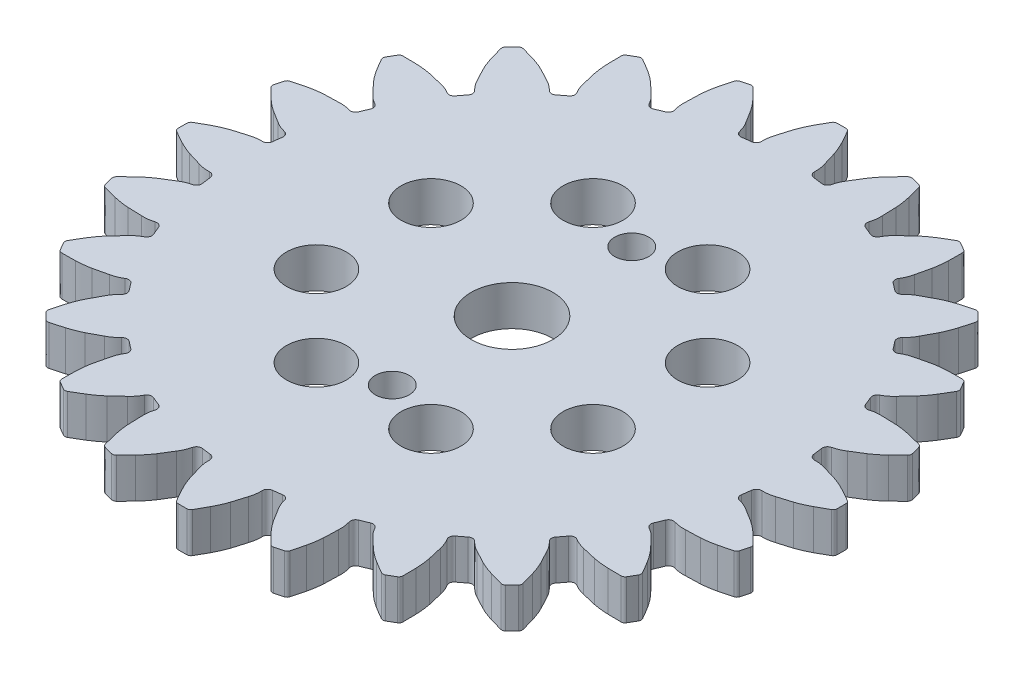
SolidWorks part; units mm, degrees
ref_plane "Front Plane" through (0, 0, 0) normal (0, 0, 1) x (1, 0, 0)
ref_plane "Top Plane" through (0, 0, 0) normal (0, 1, 0) x (1, 0, 0)
ref_plane "Right Plane" through (0, 0, 0) normal (1, 0, 0) x (0, 0, -1)
sketch "Sketch1" plane through (0, 0, 0) normal (0, 1, 0) x (1, 0, 0)
  line L0 (609.6, 337.82) -> (609.6, 271.78) construction
  line L1 (642.62, 304.8) -> (576.58, 304.8) construction
  arc A0 (636.7268, 307.9141) -> (636.6714, 308.364) centre (609.6, 304.8) ccw
  arc A1 (638.4674, 307.2733) -> (637.2762, 307.4442) centre (637.4121, 304.1554) ccw
  arc A2 (639.8524, 306.8554) -> (638.4674, 307.2733) centre (-758.3943, -4324.3767) ccw
  arc A3 (641.238, 306.2479) -> (639.8524, 306.8554) centre (637.042, 298.5613) ccw
  arc A4 (642.4176, 305.5857) -> (641.238, 306.2479) centre (614.8356, 257.8343) ccw
  arc A5 (642.62, 304.8) -> (642.617, 305.2456) centre (609.6, 304.8) ccw
  arc A6 (642.617, 305.2456) -> (642.4176, 305.5857) centre (642.218, 305.2402) ccw
  arc A7 (636.7268, 307.9141) -> (637.2762, 307.4442) centre (637.2542, 307.9746) ccw
  arc A8 (636.6714, 301.236) -> (636.7268, 301.6859) centre (609.6, 304.8) ccw
  arc A9 (637.2762, 302.1558) -> (638.4674, 302.3267) centre (637.4121, 305.4446) ccw
  arc A10 (638.4674, 302.3267) -> (639.8524, 302.7446) centre (-758.3943, 4933.9767) ccw
  arc A11 (639.8524, 302.7446) -> (641.238, 303.3521) centre (637.042, 311.0387) ccw
  arc A12 (641.238, 303.3521) -> (642.4176, 304.0143) centre (614.8356, 351.7657) ccw
  arc A13 (642.617, 304.3544) -> (642.62, 304.8) centre (609.6, 304.8) ccw
  arc A14 (642.4176, 304.0143) -> (642.617, 304.3544) centre (642.218, 304.3598) ccw
  arc A15 (637.2762, 302.1558) -> (636.7268, 301.6859) centre (637.2542, 301.6254) ccw
  arc A16 (636.6085, 300.787) -> (636.6714, 301.236) centre (609.6, 304.8) ccw
  arc A17 (638.1239, 299.7175) -> (637.0175, 300.191) centre (636.2976, 296.9791) ccw
  arc A18 (639.3535, 298.9554) -> (638.1239, 299.7175) centre (-1909.9001, -3812.5784) ccw
  arc A19 (640.5347, 298.01) -> (639.3535, 298.9554) centre (634.4923, 291.6714) ccw
  arc A20 (641.5027, 297.0651) -> (640.5347, 298.01) centre (602.5015, 258.0796) ccw
  arc A21 (641.4949, 296.2538) -> (641.6073, 296.6849) centre (609.6, 304.8) ccw
  arc A22 (641.6073, 296.6849) -> (641.5027, 297.0651) centre (641.2205, 296.783) ccw
  arc A23 (636.6085, 300.787) -> (637.0175, 300.191) centre (637.1336, 300.709) ccw
  arc A24 (634.8265, 294.3508) -> (634.9965, 294.7711) centre (609.6, 304.8) ccw
  arc A25 (635.6488, 295.0828) -> (636.8437, 294.9396) centre (636.6313, 298.2243) ccw
  arc A26 (636.8437, 294.9396) -> (638.2896, 294.9848) centre (486.3381, 5130.3043) ccw
  arc A27 (638.2896, 294.9848) -> (639.7852, 295.2129) centre (637.7216, 303.7236) ccw
  arc A28 (639.7852, 295.2129) -> (641.096, 295.5473) centre (626.8128, 348.8103) ccw
  arc A29 (641.3766, 295.8242) -> (641.4949, 296.2538) centre (609.6, 304.8) ccw
  arc A30 (641.096, 295.5473) -> (641.3766, 295.8242) centre (640.9927, 295.9327) ccw
  arc A31 (635.6488, 295.0828) -> (634.9965, 294.7711) centre (635.4903, 294.5761) ccw
  arc A32 (634.6496, 293.9334) -> (634.8265, 294.3508) centre (609.6, 304.8) ccw
  arc A33 (635.8366, 292.5082) -> (634.8904, 293.2519) centre (633.3637, 290.3357) ccw
  arc A34 (636.827, 291.4538) -> (635.8366, 292.5082) centre (-2889.7061, -3020.1875) ccw
  arc A35 (637.7232, 290.2349) -> (636.827, 291.4538) centre (630.2462, 285.6761) ccw
  arc A36 (638.4137, 289.0716) -> (637.7232, 290.2349) centre (590.6513, 261.5087) ccw
  arc A37 (638.1962, 288.29) -> (638.4163, 288.6774) centre (609.6, 304.8) ccw
  arc A38 (638.4163, 288.6774) -> (638.4137, 289.0716) centre (638.0681, 288.8722) ccw
  arc A39 (634.6496, 293.9334) -> (634.8904, 293.2519) centre (635.1366, 293.7222) ccw
  arc A40 (631.2625, 288.1778) -> (631.5355, 288.5397) centre (609.6, 304.8) ccw
  arc A41 (632.2462, 288.672) -> (633.3633, 288.2244) centre (634.0083, 291.4522) ccw
  arc A42 (633.3633, 288.2244) -> (634.7717, 287.8938) centre (1739.4706, 4997.7818) ccw
  arc A43 (634.7717, 287.8938) -> (636.2753, 287.7271) centre (636.4848, 296.4818) ccw
  arc A44 (636.2753, 287.7271) -> (637.6281, 287.7108) centre (637.617, 342.8557) ccw
  arc A45 (637.9708, 287.9056) -> (638.1962, 288.29) centre (609.6, 304.8) ccw
  arc A46 (637.6281, 287.7108) -> (637.9708, 287.9056) centre (637.628, 288.1098) ccw
  arc A47 (632.2462, 288.672) -> (631.5355, 288.5397) centre (631.962, 288.2236) ccw
  arc A48 (630.9836, 287.8204) -> (631.2625, 288.1778) centre (609.6, 304.8) ccw
  arc A49 (631.7612, 286.1365) -> (631.0397, 287.0997) centre (628.8104, 284.6781) ccw
  arc A50 (632.445, 284.8617) -> (631.7612, 286.1365) centre (-3631.0403, -2001.2042) ccw
  arc A51 (632.9952, 283.4524) -> (632.445, 284.8617) centre (624.593, 280.9842) ccw
  arc A52 (633.3611, 282.15) -> (632.9952, 283.4524) centre (580.0923, 267.8881) ccw
  arc A53 (632.9487, 281.4513) -> (633.2616, 281.7685) centre (609.6, 304.8) ccw
  arc A54 (633.2616, 281.7685) -> (633.3611, 282.15) centre (632.9757, 282.0468) ccw
  arc A55 (630.9836, 287.8204) -> (631.0397, 287.0997) centre (631.3993, 287.4903) ccw
  arc A56 (626.2222, 283.1375) -> (626.5796, 283.4164) centre (609.6, 304.8) ccw
  arc A57 (627.3003, 283.3603) -> (628.2635, 282.6388) centre (629.7219, 285.5896) ccw
  arc A58 (628.2635, 282.6388) -> (629.5383, 281.955) centre (2915.6042, 4545.4403) ccw
  arc A59 (629.5383, 281.955) -> (630.9476, 281.4048) centre (633.4158, 289.807) ccw
  arc A60 (630.9476, 281.4048) -> (632.25, 281.0389) centre (646.5119, 334.3077) ccw
  arc A61 (632.6315, 281.1384) -> (632.9487, 281.4513) centre (609.6, 304.8) ccw
  arc A62 (632.25, 281.0389) -> (632.6315, 281.1384) centre (632.3532, 281.4243) ccw
  arc A63 (627.3003, 283.3603) -> (626.5796, 283.4164) centre (626.9097, 283.0007) ccw
  arc A64 (625.8603, 282.8645) -> (626.2222, 283.1375) centre (609.6, 304.8) ccw
  arc A65 (626.1756, 281.0367) -> (625.728, 282.1538) centre (622.9478, 280.3917) ccw
  arc A66 (626.5062, 279.6283) -> (626.1756, 281.0367) centre (-4083.3818, -825.0706) ccw
  arc A67 (626.6729, 278.1247) -> (626.5062, 279.6283) centre (617.9182, 277.9152) ccw
  arc A68 (626.6892, 276.7719) -> (626.6729, 278.1247) centre (571.5443, 276.783) ccw
  arc A69 (626.11, 276.2038) -> (626.4944, 276.4292) centre (609.6, 304.8) ccw
  arc A70 (626.4944, 276.4292) -> (626.6892, 276.7719) centre (626.2902, 276.772) ccw
  arc A71 (625.8603, 282.8645) -> (625.728, 282.1538) centre (626.1764, 282.438) ccw
  arc A72 (620.0492, 279.5735) -> (620.4666, 279.7504) centre (609.6, 304.8) ccw
  arc A73 (621.1481, 279.5096) -> (621.8918, 278.5634) centre (624.0643, 281.0363) ccw
  arc A74 (621.8918, 278.5634) -> (622.9462, 277.573) centre (3934.5875, 3804.1061) ccw
  arc A75 (622.9462, 277.573) -> (624.1651, 276.6768) centre (628.7239, 284.1538) ccw
  arc A76 (624.1651, 276.6768) -> (625.3284, 275.9863) centre (652.8913, 323.7487) ccw
  arc A77 (625.7226, 275.9837) -> (626.11, 276.2038) centre (609.6, 304.8) ccw
  arc A78 (625.3284, 275.9863) -> (625.7226, 275.9837) centre (625.5278, 276.3319) ccw
  arc A79 (621.1481, 279.5096) -> (620.4666, 279.7504) centre (620.6778, 279.2634) ccw
  arc A80 (619.6289, 279.4035) -> (620.0492, 279.5735) centre (609.6, 304.8) ccw
  arc A81 (619.4604, 277.5563) -> (619.3172, 278.7512) centre (616.1757, 277.7687) ccw
  arc A82 (619.4152, 276.1104) -> (619.4604, 277.5563) centre (-4215.9043, 428.0619) ccw
  arc A83 (619.1871, 274.6148) -> (619.4152, 276.1104) centre (610.6764, 276.6784) ccw
  arc A84 (618.8527, 273.304) -> (619.1871, 274.6148) centre (565.5897, 287.5872) ccw
  arc A85 (618.1462, 272.9051) -> (618.5758, 273.0234) centre (609.6, 304.8) ccw
  arc A86 (618.5758, 273.0234) -> (618.8527, 273.304) centre (618.4673, 273.4073) ccw
  arc A87 (619.6289, 279.4035) -> (619.3172, 278.7512) centre (619.8239, 278.9097) ccw
  arc A88 (613.164, 277.7286) -> (613.613, 277.7915) centre (609.6, 304.8) ccw
  arc A89 (614.209, 277.3825) -> (614.6825, 276.2761) centre (617.4209, 278.1024) ccw
  arc A90 (614.6825, 276.2761) -> (615.4446, 275.0465) centre (4726.9784, 2824.3001) ccw
  arc A91 (615.4446, 275.0465) -> (616.39, 273.8653) centre (622.7286, 279.9077) ccw
  arc A92 (616.39, 273.8653) -> (617.3349, 272.8973) centre (656.3204, 311.8985) ccw
  arc A93 (617.7151, 272.7927) -> (618.1462, 272.9051) centre (609.6, 304.8) ccw
  arc A94 (617.3349, 272.8973) -> (617.7151, 272.7927) centre (617.617, 273.1795) ccw
  arc A95 (614.209, 277.3825) -> (613.613, 277.7915) centre (613.691, 277.2664) ccw
  arc A96 (612.7141, 277.6732) -> (613.164, 277.7286) centre (609.6, 304.8) ccw
  arc A97 (612.0733, 275.9326) -> (612.2442, 277.1238) centre (608.9554, 276.9879) ccw
  arc A98 (611.6554, 274.5476) -> (612.0733, 275.9326) centre (-4019.5767, 1672.7943) ccw
  arc A99 (611.0479, 273.162) -> (611.6554, 274.5476) centre (603.3613, 277.358) ccw
  arc A100 (610.3857, 271.9824) -> (611.0479, 273.162) centre (562.6343, 299.5644) ccw
  arc A101 (609.6, 271.78) -> (610.0456, 271.783) centre (609.6, 304.8) ccw
  arc A102 (610.0456, 271.783) -> (610.3857, 271.9824) centre (610.0402, 272.182) ccw
  arc A103 (612.7141, 277.6732) -> (612.2442, 277.1238) centre (612.7746, 277.1458) ccw
  arc A104 (606.036, 277.7286) -> (606.4859, 277.6732) centre (609.6, 304.8) ccw
  arc A105 (606.9558, 277.1238) -> (607.1267, 275.9326) centre (610.2446, 276.9879) ccw
  arc A106 (607.1267, 275.9326) -> (607.5446, 274.5476) centre (5238.7767, 1672.7943) ccw
  arc A107 (607.5446, 274.5476) -> (608.1521, 273.162) centre (615.8387, 277.358) ccw
  arc A108 (608.1521, 273.162) -> (608.8143, 271.9824) centre (656.5657, 299.5644) ccw
  arc A109 (609.1544, 271.783) -> (609.6, 271.78) centre (609.6, 304.8) ccw
  arc A110 (608.8143, 271.9824) -> (609.1544, 271.783) centre (609.1598, 272.182) ccw
  arc A111 (606.9558, 277.1238) -> (606.4859, 277.6732) centre (606.4254, 277.1458) ccw
  arc A112 (605.587, 277.7915) -> (606.036, 277.7286) centre (609.6, 304.8) ccw
  arc A113 (604.5175, 276.2761) -> (604.991, 277.3825) centre (601.7791, 278.1024) ccw
  arc A114 (603.7554, 275.0465) -> (604.5175, 276.2761) centre (-3507.7784, 2824.3001) ccw
  arc A115 (602.81, 273.8653) -> (603.7554, 275.0465) centre (596.4714, 279.9077) ccw
  arc A116 (601.8651, 272.8973) -> (602.81, 273.8653) centre (562.8796, 311.8985) ccw
  arc A117 (601.0538, 272.9051) -> (601.4849, 272.7927) centre (609.6, 304.8) ccw
  arc A118 (601.4849, 272.7927) -> (601.8651, 272.8973) centre (601.583, 273.1795) ccw
  arc A119 (605.587, 277.7915) -> (604.991, 277.3825) centre (605.509, 277.2664) ccw
  arc A120 (599.1508, 279.5735) -> (599.5711, 279.4035) centre (609.6, 304.8) ccw
  arc A121 (599.8828, 278.7512) -> (599.7396, 277.5563) centre (603.0243, 277.7687) ccw
  arc A122 (599.7396, 277.5563) -> (599.7848, 276.1104) centre (5435.1043, 428.0619) ccw
  arc A123 (599.7848, 276.1104) -> (600.0129, 274.6148) centre (608.5236, 276.6784) ccw
  arc A124 (600.0129, 274.6148) -> (600.3473, 273.304) centre (653.6103, 287.5872) ccw
  arc A125 (600.6242, 273.0234) -> (601.0538, 272.9051) centre (609.6, 304.8) ccw
  arc A126 (600.3473, 273.304) -> (600.6242, 273.0234) centre (600.7327, 273.4073) ccw
  arc A127 (599.8828, 278.7512) -> (599.5711, 279.4035) centre (599.3761, 278.9097) ccw
  arc A128 (598.7334, 279.7504) -> (599.1508, 279.5735) centre (609.6, 304.8) ccw
  arc A129 (597.3082, 278.5634) -> (598.0519, 279.5096) centre (595.1357, 281.0363) ccw
  arc A130 (596.2538, 277.573) -> (597.3082, 278.5634) centre (-2715.3875, 3804.1061) ccw
  arc A131 (595.0349, 276.6768) -> (596.2538, 277.573) centre (590.4761, 284.1538) ccw
  arc A132 (593.8716, 275.9863) -> (595.0349, 276.6768) centre (566.3087, 323.7487) ccw
  arc A133 (593.09, 276.2038) -> (593.4774, 275.9837) centre (609.6, 304.8) ccw
  arc A134 (593.4774, 275.9837) -> (593.8716, 275.9863) centre (593.6722, 276.3319) ccw
  arc A135 (598.7334, 279.7504) -> (598.0519, 279.5096) centre (598.5222, 279.2634) ccw
  arc A136 (592.9778, 283.1375) -> (593.3397, 282.8645) centre (609.6, 304.8) ccw
  arc A137 (593.472, 282.1538) -> (593.0244, 281.0367) centre (596.2522, 280.3917) ccw
  arc A138 (593.0244, 281.0367) -> (592.6938, 279.6283) centre (5302.5818, -825.0706) ccw
  arc A139 (592.6938, 279.6283) -> (592.5271, 278.1247) centre (601.2818, 277.9152) ccw
  arc A140 (592.5271, 278.1247) -> (592.5108, 276.7719) centre (647.6557, 276.783) ccw
  arc A141 (592.7056, 276.4292) -> (593.09, 276.2038) centre (609.6, 304.8) ccw
  arc A142 (592.5108, 276.7719) -> (592.7056, 276.4292) centre (592.9098, 276.772) ccw
  arc A143 (593.472, 282.1538) -> (593.3397, 282.8645) centre (593.0236, 282.438) ccw
  arc A144 (592.6204, 283.4164) -> (592.9778, 283.1375) centre (609.6, 304.8) ccw
  arc A145 (590.9365, 282.6388) -> (591.8997, 283.3603) centre (589.4781, 285.5896) ccw
  arc A146 (589.6617, 281.955) -> (590.9365, 282.6388) centre (-1696.4042, 4545.4403) ccw
  arc A147 (588.2524, 281.4048) -> (589.6617, 281.955) centre (585.7842, 289.807) ccw
  arc A148 (586.95, 281.0389) -> (588.2524, 281.4048) centre (572.6881, 334.3077) ccw
  arc A149 (586.2513, 281.4513) -> (586.5685, 281.1384) centre (609.6, 304.8) ccw
  arc A150 (586.5685, 281.1384) -> (586.95, 281.0389) centre (586.8468, 281.4243) ccw
  arc A151 (592.6204, 283.4164) -> (591.8997, 283.3603) centre (592.2903, 283.0007) ccw
  arc A152 (587.9375, 288.1778) -> (588.2164, 287.8204) centre (609.6, 304.8) ccw
  arc A153 (588.1603, 287.0997) -> (587.4388, 286.1365) centre (590.3896, 284.6781) ccw
  arc A154 (587.4388, 286.1365) -> (586.755, 284.8617) centre (4850.2403, -2001.2042) ccw
  arc A155 (586.755, 284.8617) -> (586.2048, 283.4524) centre (594.607, 280.9842) ccw
  arc A156 (586.2048, 283.4524) -> (585.8389, 282.15) centre (639.1077, 267.8881) ccw
  arc A157 (585.9384, 281.7685) -> (586.2513, 281.4513) centre (609.6, 304.8) ccw
  arc A158 (585.8389, 282.15) -> (585.9384, 281.7685) centre (586.2243, 282.0468) ccw
  arc A159 (588.1603, 287.0997) -> (588.2164, 287.8204) centre (587.8007, 287.4903) ccw
  arc A160 (587.6645, 288.5397) -> (587.9375, 288.1778) centre (609.6, 304.8) ccw
  arc A161 (585.8367, 288.2244) -> (586.9538, 288.672) centre (585.1917, 291.4522) ccw
  arc A162 (584.4283, 287.8938) -> (585.8367, 288.2244) centre (-520.2706, 4997.7818) ccw
  arc A163 (582.9247, 287.7271) -> (584.4283, 287.8938) centre (582.7152, 296.4818) ccw
  arc A164 (581.5719, 287.7108) -> (582.9247, 287.7271) centre (581.583, 342.8557) ccw
  arc A165 (581.0038, 288.29) -> (581.2292, 287.9056) centre (609.6, 304.8) ccw
  arc A166 (581.2292, 287.9056) -> (581.5719, 287.7108) centre (581.572, 288.1098) ccw
  arc A167 (587.6645, 288.5397) -> (586.9538, 288.672) centre (587.238, 288.2236) ccw
  arc A168 (584.3735, 294.3508) -> (584.5504, 293.9334) centre (609.6, 304.8) ccw
  arc A169 (584.3096, 293.2519) -> (583.3634, 292.5082) centre (585.8363, 290.3357) ccw
  arc A170 (583.3634, 292.5082) -> (582.373, 291.4538) centre (4108.9061, -3020.1875) ccw
  arc A171 (582.373, 291.4538) -> (581.4768, 290.2349) centre (588.9538, 285.6761) ccw
  arc A172 (581.4768, 290.2349) -> (580.7863, 289.0716) centre (628.5487, 261.5087) ccw
  arc A173 (580.7837, 288.6774) -> (581.0038, 288.29) centre (609.6, 304.8) ccw
  arc A174 (580.7863, 289.0716) -> (580.7837, 288.6774) centre (581.1319, 288.8722) ccw
  arc A175 (584.3096, 293.2519) -> (584.5504, 293.9334) centre (584.0634, 293.7222) ccw
  arc A176 (584.2035, 294.7711) -> (584.3735, 294.3508) centre (609.6, 304.8) ccw
  arc A177 (582.3563, 294.9396) -> (583.5512, 295.0828) centre (582.5687, 298.2243) ccw
  arc A178 (580.9104, 294.9848) -> (582.3563, 294.9396) centre (732.8619, 5130.3043) ccw
  arc A179 (579.4148, 295.2129) -> (580.9104, 294.9848) centre (581.4784, 303.7236) ccw
  arc A180 (578.104, 295.5473) -> (579.4148, 295.2129) centre (592.3872, 348.8103) ccw
  arc A181 (577.7051, 296.2538) -> (577.8234, 295.8242) centre (609.6, 304.8) ccw
  arc A182 (577.8234, 295.8242) -> (578.104, 295.5473) centre (578.2073, 295.9327) ccw
  arc A183 (584.2035, 294.7711) -> (583.5512, 295.0828) centre (583.7097, 294.5761) ccw
  arc A184 (582.5286, 301.236) -> (582.5915, 300.787) centre (609.6, 304.8) ccw
  arc A185 (582.1825, 300.191) -> (581.0761, 299.7175) centre (582.9024, 296.9791) ccw
  arc A186 (581.0761, 299.7175) -> (579.8465, 298.9554) centre (3129.1001, -3812.5784) ccw
  arc A187 (579.8465, 298.9554) -> (578.6653, 298.01) centre (584.7077, 291.6714) ccw
  arc A188 (578.6653, 298.01) -> (577.6973, 297.0651) centre (616.6985, 258.0796) ccw
  arc A189 (577.5927, 296.6849) -> (577.7051, 296.2538) centre (609.6, 304.8) ccw
  arc A190 (577.6973, 297.0651) -> (577.5927, 296.6849) centre (577.9795, 296.783) ccw
  arc A191 (582.1825, 300.191) -> (582.5915, 300.787) centre (582.0664, 300.709) ccw
  arc A192 (582.4732, 301.6859) -> (582.5286, 301.236) centre (609.6, 304.8) ccw
  arc A193 (580.7326, 302.3267) -> (581.9238, 302.1558) centre (581.7879, 305.4446) ccw
  arc A194 (579.3476, 302.7446) -> (580.7326, 302.3267) centre (1977.5943, 4933.9767) ccw
  arc A195 (577.962, 303.3521) -> (579.3476, 302.7446) centre (582.158, 311.0387) ccw
  arc A196 (576.7824, 304.0143) -> (577.962, 303.3521) centre (604.3644, 351.7657) ccw
  arc A197 (576.58, 304.8) -> (576.583, 304.3544) centre (609.6, 304.8) ccw
  arc A198 (576.583, 304.3544) -> (576.7824, 304.0143) centre (576.982, 304.3598) ccw
  arc A199 (582.4732, 301.6859) -> (581.9238, 302.1558) centre (581.9458, 301.6254) ccw
  arc A200 (582.5286, 308.364) -> (582.4732, 307.9141) centre (609.6, 304.8) ccw
  arc A201 (581.9238, 307.4442) -> (580.7326, 307.2733) centre (581.7879, 304.1554) ccw
  arc A202 (580.7326, 307.2733) -> (579.3476, 306.8554) centre (1977.5943, -4324.3767) ccw
  arc A203 (579.3476, 306.8554) -> (577.962, 306.2479) centre (582.158, 298.5613) ccw
  arc A204 (577.962, 306.2479) -> (576.7824, 305.5857) centre (604.3644, 257.8343) ccw
  arc A205 (576.583, 305.2456) -> (576.58, 304.8) centre (609.6, 304.8) ccw
  arc A206 (576.7824, 305.5857) -> (576.583, 305.2456) centre (576.982, 305.2402) ccw
  arc A207 (581.9238, 307.4442) -> (582.4732, 307.9141) centre (581.9458, 307.9746) ccw
  arc A208 (582.5915, 308.813) -> (582.5286, 308.364) centre (609.6, 304.8) ccw
  arc A209 (581.0761, 309.8825) -> (582.1825, 309.409) centre (582.9024, 312.6209) ccw
  arc A210 (579.8465, 310.6446) -> (581.0761, 309.8825) centre (3129.1001, 4422.1784) ccw
  arc A211 (578.6653, 311.59) -> (579.8465, 310.6446) centre (584.7077, 317.9286) ccw
  arc A212 (577.6973, 312.5349) -> (578.6653, 311.59) centre (616.6985, 351.5204) ccw
  arc A213 (577.7051, 313.3462) -> (577.5927, 312.9151) centre (609.6, 304.8) ccw
  arc A214 (577.5927, 312.9151) -> (577.6973, 312.5349) centre (577.9795, 312.817) ccw
  arc A215 (582.5915, 308.813) -> (582.1825, 309.409) centre (582.0664, 308.891) ccw
  arc A216 (584.3735, 315.2492) -> (584.2035, 314.8289) centre (609.6, 304.8) ccw
  arc A217 (583.5512, 314.5172) -> (582.3563, 314.6604) centre (582.5687, 311.3757) ccw
  arc A218 (582.3563, 314.6604) -> (580.9104, 314.6152) centre (732.8619, -4520.7043) ccw
  arc A219 (580.9104, 314.6152) -> (579.4148, 314.3871) centre (581.4784, 305.8764) ccw
  arc A220 (579.4148, 314.3871) -> (578.104, 314.0527) centre (592.3872, 260.7897) ccw
  arc A221 (577.8234, 313.7758) -> (577.7051, 313.3462) centre (609.6, 304.8) ccw
  arc A222 (578.104, 314.0527) -> (577.8234, 313.7758) centre (578.2073, 313.6673) ccw
  arc A223 (583.5512, 314.5172) -> (584.2035, 314.8289) centre (583.7097, 315.0239) ccw
  arc A224 (584.5504, 315.6666) -> (584.3735, 315.2492) centre (609.6, 304.8) ccw
  arc A225 (583.3634, 317.0918) -> (584.3096, 316.3481) centre (585.8363, 319.2643) ccw
  arc A226 (582.373, 318.1462) -> (583.3634, 317.0918) centre (4108.9061, 3629.7875) ccw
  arc A227 (581.4768, 319.3651) -> (582.373, 318.1462) centre (588.9538, 323.9239) ccw
  arc A228 (580.7863, 320.5284) -> (581.4768, 319.3651) centre (628.5487, 348.0913) ccw
  arc A229 (581.0038, 321.31) -> (580.7837, 320.9226) centre (609.6, 304.8) ccw
  arc A230 (580.7837, 320.9226) -> (580.7863, 320.5284) centre (581.1319, 320.7278) ccw
  arc A231 (584.5504, 315.6666) -> (584.3096, 316.3481) centre (584.0634, 315.8778) ccw
  arc A232 (587.9375, 321.4222) -> (587.6645, 321.0603) centre (609.6, 304.8) ccw
  arc A233 (586.9538, 320.928) -> (585.8367, 321.3756) centre (585.1917, 318.1478) ccw
  arc A234 (585.8367, 321.3756) -> (584.4283, 321.7062) centre (-520.2706, -4388.1818) ccw
  arc A235 (584.4283, 321.7062) -> (582.9247, 321.8729) centre (582.7152, 313.1182) ccw
  arc A236 (582.9247, 321.8729) -> (581.5719, 321.8892) centre (581.583, 266.7443) ccw
  arc A237 (581.2292, 321.6944) -> (581.0038, 321.31) centre (609.6, 304.8) ccw
  arc A238 (581.5719, 321.8892) -> (581.2292, 321.6944) centre (581.572, 321.4902) ccw
  arc A239 (586.9538, 320.928) -> (587.6645, 321.0603) centre (587.238, 321.3764) ccw
  arc A240 (588.2164, 321.7796) -> (587.9375, 321.4222) centre (609.6, 304.8) ccw
  arc A241 (587.4388, 323.4635) -> (588.1603, 322.5003) centre (590.3896, 324.9219) ccw
  arc A242 (586.755, 324.7383) -> (587.4388, 323.4635) centre (4850.2403, 2610.8042) ccw
  arc A243 (586.2048, 326.1476) -> (586.755, 324.7383) centre (594.607, 328.6158) ccw
  arc A244 (585.8389, 327.45) -> (586.2048, 326.1476) centre (639.1077, 341.7119) ccw
  arc A245 (586.2513, 328.1487) -> (585.9384, 327.8315) centre (609.6, 304.8) ccw
  arc A246 (585.9384, 327.8315) -> (585.8389, 327.45) centre (586.2243, 327.5532) ccw
  arc A247 (588.2164, 321.7796) -> (588.1603, 322.5003) centre (587.8007, 322.1097) ccw
  arc A248 (592.9778, 326.4625) -> (592.6204, 326.1836) centre (609.6, 304.8) ccw
  arc A249 (591.8997, 326.2397) -> (590.9365, 326.9612) centre (589.4781, 324.0104) ccw
  arc A250 (590.9365, 326.9612) -> (589.6617, 327.645) centre (-1696.4042, -3935.8403) ccw
  arc A251 (589.6617, 327.645) -> (588.2524, 328.1952) centre (585.7842, 319.793) ccw
  arc A252 (588.2524, 328.1952) -> (586.95, 328.5611) centre (572.6881, 275.2923) ccw
  arc A253 (586.5685, 328.4616) -> (586.2513, 328.1487) centre (609.6, 304.8) ccw
  arc A254 (586.95, 328.5611) -> (586.5685, 328.4616) centre (586.8468, 328.1757) ccw
  arc A255 (591.8997, 326.2397) -> (592.6204, 326.1836) centre (592.2903, 326.5993) ccw
  arc A256 (593.3397, 326.7355) -> (592.9778, 326.4625) centre (609.6, 304.8) ccw
  arc A257 (593.0244, 328.5633) -> (593.472, 327.4462) centre (596.2522, 329.2083) ccw
  arc A258 (592.6938, 329.9717) -> (593.0244, 328.5633) centre (5302.5818, 1434.6706) ccw
  arc A259 (592.5271, 331.4753) -> (592.6938, 329.9717) centre (601.2818, 331.6848) ccw
  arc A260 (592.5108, 332.8281) -> (592.5271, 331.4753) centre (647.6557, 332.817) ccw
  arc A261 (593.09, 333.3962) -> (592.7056, 333.1708) centre (609.6, 304.8) ccw
  arc A262 (592.7056, 333.1708) -> (592.5108, 332.8281) centre (592.9098, 332.828) ccw
  arc A263 (593.3397, 326.7355) -> (593.472, 327.4462) centre (593.0236, 327.162) ccw
  arc A264 (599.1508, 330.0265) -> (598.7334, 329.8496) centre (609.6, 304.8) ccw
  arc A265 (598.0519, 330.0904) -> (597.3082, 331.0366) centre (595.1357, 328.5637) ccw
  arc A266 (597.3082, 331.0366) -> (596.2538, 332.027) centre (-2715.3875, -3194.5061) ccw
  arc A267 (596.2538, 332.027) -> (595.0349, 332.9232) centre (590.4761, 325.4462) ccw
  arc A268 (595.0349, 332.9232) -> (593.8716, 333.6137) centre (566.3087, 285.8513) ccw
  arc A269 (593.4774, 333.6163) -> (593.09, 333.3962) centre (609.6, 304.8) ccw
  arc A270 (593.8716, 333.6137) -> (593.4774, 333.6163) centre (593.6722, 333.2681) ccw
  arc A271 (598.0519, 330.0904) -> (598.7334, 329.8496) centre (598.5222, 330.3366) ccw
  arc A272 (599.5711, 330.1965) -> (599.1508, 330.0265) centre (609.6, 304.8) ccw
  arc A273 (599.7396, 332.0437) -> (599.8828, 330.8488) centre (603.0243, 331.8313) ccw
  arc A274 (599.7848, 333.4896) -> (599.7396, 332.0437) centre (5435.1043, 181.5381) ccw
  arc A275 (600.0129, 334.9852) -> (599.7848, 333.4896) centre (608.5236, 332.9216) ccw
  arc A276 (600.3473, 336.296) -> (600.0129, 334.9852) centre (653.6103, 322.0128) ccw
  arc A277 (601.0538, 336.6949) -> (600.6242, 336.5766) centre (609.6, 304.8) ccw
  arc A278 (600.6242, 336.5766) -> (600.3473, 336.296) centre (600.7327, 336.1927) ccw
  arc A279 (599.5711, 330.1965) -> (599.8828, 330.8488) centre (599.3761, 330.6903) ccw
  arc A280 (606.036, 331.8714) -> (605.587, 331.8085) centre (609.6, 304.8) ccw
  arc A281 (604.991, 332.2175) -> (604.5175, 333.3239) centre (601.7791, 331.4976) ccw
  arc A282 (604.5175, 333.3239) -> (603.7554, 334.5535) centre (-3507.7784, -2214.7001) ccw
  arc A283 (603.7554, 334.5535) -> (602.81, 335.7347) centre (596.4714, 329.6923) ccw
  arc A284 (602.81, 335.7347) -> (601.8651, 336.7027) centre (562.8796, 297.7015) ccw
  arc A285 (601.4849, 336.8073) -> (601.0538, 336.6949) centre (609.6, 304.8) ccw
  arc A286 (601.8651, 336.7027) -> (601.4849, 336.8073) centre (601.583, 336.4205) ccw
  arc A287 (604.991, 332.2175) -> (605.587, 331.8085) centre (605.509, 332.3336) ccw
  arc A288 (606.4859, 331.9268) -> (606.036, 331.8714) centre (609.6, 304.8) ccw
  arc A289 (607.1267, 333.6674) -> (606.9558, 332.4762) centre (610.2446, 332.6121) ccw
  arc A290 (607.5446, 335.0524) -> (607.1267, 333.6674) centre (5238.7767, -1063.1943) ccw
  arc A291 (608.1521, 336.438) -> (607.5446, 335.0524) centre (615.8387, 332.242) ccw
  arc A292 (608.8143, 337.6176) -> (608.1521, 336.438) centre (656.5657, 310.0356) ccw
  arc A293 (609.6, 337.82) -> (609.1544, 337.817) centre (609.6, 304.8) ccw
  arc A294 (609.1544, 337.817) -> (608.8143, 337.6176) centre (609.1598, 337.418) ccw
  arc A295 (606.4859, 331.9268) -> (606.9558, 332.4762) centre (606.4254, 332.4542) ccw
  arc A296 (613.164, 331.8714) -> (612.7141, 331.9268) centre (609.6, 304.8) ccw
  arc A297 (612.2442, 332.4762) -> (612.0733, 333.6674) centre (608.9554, 332.6121) ccw
  arc A298 (612.0733, 333.6674) -> (611.6554, 335.0524) centre (-4019.5767, -1063.1943) ccw
  arc A299 (611.6554, 335.0524) -> (611.0479, 336.438) centre (603.3613, 332.242) ccw
  arc A300 (611.0479, 336.438) -> (610.3857, 337.6176) centre (562.6343, 310.0356) ccw
  arc A301 (610.0456, 337.817) -> (609.6, 337.82) centre (609.6, 304.8) ccw
  arc A302 (610.3857, 337.6176) -> (610.0456, 337.817) centre (610.0402, 337.418) ccw
  arc A303 (612.2442, 332.4762) -> (612.7141, 331.9268) centre (612.7746, 332.4542) ccw
  arc A304 (613.613, 331.8085) -> (613.164, 331.8714) centre (609.6, 304.8) ccw
  arc A305 (614.6825, 333.3239) -> (614.209, 332.2175) centre (617.4209, 331.4976) ccw
  arc A306 (615.4446, 334.5535) -> (614.6825, 333.3239) centre (4726.9784, -2214.7001) ccw
  arc A307 (616.39, 335.7347) -> (615.4446, 334.5535) centre (622.7286, 329.6923) ccw
  arc A308 (617.3349, 336.7027) -> (616.39, 335.7347) centre (656.3204, 297.7015) ccw
  arc A309 (618.1462, 336.6949) -> (617.7151, 336.8073) centre (609.6, 304.8) ccw
  arc A310 (617.7151, 336.8073) -> (617.3349, 336.7027) centre (617.617, 336.4205) ccw
  arc A311 (613.613, 331.8085) -> (614.209, 332.2175) centre (613.691, 332.3336) ccw
  arc A312 (620.0492, 330.0265) -> (619.6289, 330.1965) centre (609.6, 304.8) ccw
  arc A313 (619.3172, 330.8488) -> (619.4604, 332.0437) centre (616.1757, 331.8313) ccw
  arc A314 (619.4604, 332.0437) -> (619.4152, 333.4896) centre (-4215.9043, 181.5381) ccw
  arc A315 (619.4152, 333.4896) -> (619.1871, 334.9852) centre (610.6764, 332.9216) ccw
  arc A316 (619.1871, 334.9852) -> (618.8527, 336.296) centre (565.5897, 322.0128) ccw
  arc A317 (618.5758, 336.5766) -> (618.1462, 336.6949) centre (609.6, 304.8) ccw
  arc A318 (618.8527, 336.296) -> (618.5758, 336.5766) centre (618.4673, 336.1927) ccw
  arc A319 (619.3172, 330.8488) -> (619.6289, 330.1965) centre (619.8239, 330.6903) ccw
  arc A320 (620.4666, 329.8496) -> (620.0492, 330.0265) centre (609.6, 304.8) ccw
  arc A321 (621.8918, 331.0366) -> (621.1481, 330.0904) centre (624.0643, 328.5637) ccw
  arc A322 (622.9462, 332.027) -> (621.8918, 331.0366) centre (3934.5875, -3194.5061) ccw
  arc A323 (624.1651, 332.9232) -> (622.9462, 332.027) centre (628.7239, 325.4462) ccw
  arc A324 (625.3284, 333.6137) -> (624.1651, 332.9232) centre (652.8913, 285.8513) ccw
  arc A325 (626.11, 333.3962) -> (625.7226, 333.6163) centre (609.6, 304.8) ccw
  arc A326 (625.7226, 333.6163) -> (625.3284, 333.6137) centre (625.5278, 333.2681) ccw
  arc A327 (620.4666, 329.8496) -> (621.1481, 330.0904) centre (620.6778, 330.3366) ccw
  arc A328 (626.2222, 326.4625) -> (625.8603, 326.7355) centre (609.6, 304.8) ccw
  arc A329 (625.728, 327.4462) -> (626.1756, 328.5633) centre (622.9478, 329.2083) ccw
  arc A330 (626.1756, 328.5633) -> (626.5062, 329.9717) centre (-4083.3818, 1434.6706) ccw
  arc A331 (626.5062, 329.9717) -> (626.6729, 331.4753) centre (617.9182, 331.6848) ccw
  arc A332 (626.6729, 331.4753) -> (626.6892, 332.8281) centre (571.5443, 332.817) ccw
  arc A333 (626.4944, 333.1708) -> (626.11, 333.3962) centre (609.6, 304.8) ccw
  arc A334 (626.6892, 332.8281) -> (626.4944, 333.1708) centre (626.2902, 332.828) ccw
  arc A335 (625.728, 327.4462) -> (625.8603, 326.7355) centre (626.1764, 327.162) ccw
  arc A336 (626.5796, 326.1836) -> (626.2222, 326.4625) centre (609.6, 304.8) ccw
  arc A337 (628.2635, 326.9612) -> (627.3003, 326.2397) centre (629.7219, 324.0104) ccw
  arc A338 (629.5383, 327.645) -> (628.2635, 326.9612) centre (2915.6042, -3935.8403) ccw
  arc A339 (630.9476, 328.1952) -> (629.5383, 327.645) centre (633.4158, 319.793) ccw
  arc A340 (632.25, 328.5611) -> (630.9476, 328.1952) centre (646.5119, 275.2923) ccw
  arc A341 (632.9487, 328.1487) -> (632.6315, 328.4616) centre (609.6, 304.8) ccw
  arc A342 (632.6315, 328.4616) -> (632.25, 328.5611) centre (632.3532, 328.1757) ccw
  arc A343 (626.5796, 326.1836) -> (627.3003, 326.2397) centre (626.9097, 326.5993) ccw
  arc A344 (631.2625, 321.4222) -> (630.9836, 321.7796) centre (609.6, 304.8) ccw
  arc A345 (631.0397, 322.5003) -> (631.7612, 323.4635) centre (628.8104, 324.9219) ccw
  arc A346 (631.7612, 323.4635) -> (632.445, 324.7383) centre (-3631.0403, 2610.8042) ccw
  arc A347 (632.445, 324.7383) -> (632.9952, 326.1476) centre (624.593, 328.6158) ccw
  arc A348 (632.9952, 326.1476) -> (633.3611, 327.45) centre (580.0923, 341.7119) ccw
  arc A349 (633.2616, 327.8315) -> (632.9487, 328.1487) centre (609.6, 304.8) ccw
  arc A350 (633.3611, 327.45) -> (633.2616, 327.8315) centre (632.9757, 327.5532) ccw
  arc A351 (631.0397, 322.5003) -> (630.9836, 321.7796) centre (631.3993, 322.1097) ccw
  arc A352 (631.5355, 321.0603) -> (631.2625, 321.4222) centre (609.6, 304.8) ccw
  arc A353 (633.3633, 321.3756) -> (632.2462, 320.928) centre (634.0083, 318.1478) ccw
  arc A354 (634.7717, 321.7062) -> (633.3633, 321.3756) centre (1739.4706, -4388.1818) ccw
  arc A355 (636.2753, 321.8729) -> (634.7717, 321.7062) centre (636.4848, 313.1182) ccw
  arc A356 (637.6281, 321.8892) -> (636.2753, 321.8729) centre (637.617, 266.7443) ccw
  arc A357 (638.1962, 321.31) -> (637.9708, 321.6944) centre (609.6, 304.8) ccw
  arc A358 (637.9708, 321.6944) -> (637.6281, 321.8892) centre (637.628, 321.4902) ccw
  arc A359 (631.5355, 321.0603) -> (632.2462, 320.928) centre (631.962, 321.3764) ccw
  arc A360 (634.8265, 315.2492) -> (634.6496, 315.6666) centre (609.6, 304.8) ccw
  arc A361 (634.8904, 316.3481) -> (635.8366, 317.0918) centre (633.3637, 319.2643) ccw
  arc A362 (635.8366, 317.0918) -> (636.827, 318.1462) centre (-2889.7061, 3629.7875) ccw
  arc A363 (636.827, 318.1462) -> (637.7232, 319.3651) centre (630.2462, 323.9239) ccw
  arc A364 (637.7232, 319.3651) -> (638.4137, 320.5284) centre (590.6513, 348.0913) ccw
  arc A365 (638.4163, 320.9226) -> (638.1962, 321.31) centre (609.6, 304.8) ccw
  arc A366 (638.4137, 320.5284) -> (638.4163, 320.9226) centre (638.0681, 320.7278) ccw
  arc A367 (634.8904, 316.3481) -> (634.6496, 315.6666) centre (635.1366, 315.8778) ccw
  arc A368 (634.9965, 314.8289) -> (634.8265, 315.2492) centre (609.6, 304.8) ccw
  arc A369 (636.8437, 314.6604) -> (635.6488, 314.5172) centre (636.6313, 311.3757) ccw
  arc A370 (638.2896, 314.6152) -> (636.8437, 314.6604) centre (486.3381, -4520.7043) ccw
  arc A371 (639.7852, 314.3871) -> (638.2896, 314.6152) centre (637.7216, 305.8764) ccw
  arc A372 (641.096, 314.0527) -> (639.7852, 314.3871) centre (626.8128, 260.7897) ccw
  arc A373 (641.4949, 313.3462) -> (641.3766, 313.7758) centre (609.6, 304.8) ccw
  arc A374 (641.3766, 313.7758) -> (641.096, 314.0527) centre (640.9927, 313.6673) ccw
  arc A375 (634.9965, 314.8289) -> (635.6488, 314.5172) centre (635.4903, 315.0239) ccw
  arc A376 (636.6714, 308.364) -> (636.6085, 308.813) centre (609.6, 304.8) ccw
  arc A377 (637.0175, 309.409) -> (638.1239, 309.8825) centre (636.2976, 312.6209) ccw
  arc A378 (638.1239, 309.8825) -> (639.3535, 310.6446) centre (-1909.9001, 4422.1784) ccw
  arc A379 (639.3535, 310.6446) -> (640.5347, 311.59) centre (634.4923, 317.9286) ccw
  arc A380 (640.5347, 311.59) -> (641.5027, 312.5349) centre (602.5015, 351.5204) ccw
  arc A381 (641.6073, 312.9151) -> (641.4949, 313.3462) centre (609.6, 304.8) ccw
  arc A382 (641.5027, 312.5349) -> (641.6073, 312.9151) centre (641.2205, 312.817) ccw
  arc A383 (637.0175, 309.409) -> (636.6085, 308.813) centre (637.1336, 308.891) ccw
sketch "Sketch2" plane through (0, 0, 0) normal (0, 1, 0) x (1, 0, 0)
  circle A0 centre (609.6, 304.8) radius 4.1
  dimension "D1" = 8.2
sketch "Sketch3" plane through (0, 0, 0) normal (0, 1, 0) x (1, 0, 0)
  line L0 (598.3322, 304.8) -> (620.23, 304.8) construction
  line L1 (642.62, 304.8) -> (576.58, 304.8) construction
  line L2 (609.6, 337.82) -> (609.6, 271.78) construction
  circle A0 centre (609.6, 316.8) radius 1.7
  circle A1 centre (609.6, 292.8) radius 1.7
  dimension "D1" = 3.4
  dimension "D2" = 12
sketch "Sketch4" plane through (0, 0, 0) normal (0, 1, 0) x (1, 0, 0)
  line L0 (609.6, 304.8) -> (609.6, 339.507) construction
  line L1 (609.6, 337.82) -> (609.6, 271.78) construction
  line L2 (609.6, 304.8) -> (623.5261, 338.4207) construction
  circle A0 centre (615.3403, 318.6582) radius 3
  circle A1 centre (623.4582, 310.5403) radius 3
  circle A2 centre (623.4582, 299.0597) radius 3
  circle A3 centre (615.3403, 290.9418) radius 3
  circle A4 centre (603.8597, 290.9418) radius 3
  circle A5 centre (595.7418, 299.0597) radius 3
  circle A6 centre (595.7418, 310.5403) radius 3
  circle A7 centre (603.8597, 318.6582) radius 3
  point P24 (609.6, 304.8)
  dimension "D2" = 6
  dimension "D1" = 22.5
  dimension "D3" = 15
  dimension "D4" = 8
extrude "Boss-Extrude1" add sketch "Sketch1" along normal blind 4
extrude "Cut-Extrude2" cut sketch "Sketch2" along normal through all
extrude "Cut-Extrude3" cut sketch "Sketch3" along normal through all
extrude "Cut-Extrude4" cut sketch "Sketch4" along normal through all
